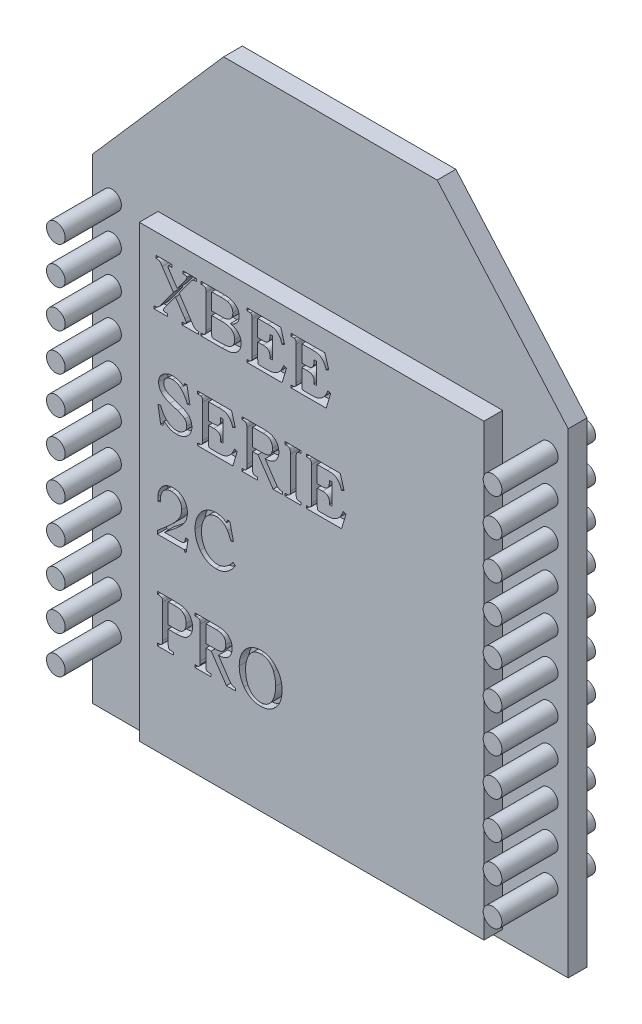
SolidWorks part; units mm, degrees
material "Custom Plastic"
ref_plane "Plan de face" through (0, 0, 0) normal (0, 0, 1) x (1, 0, 0)
ref_plane "Plan de dessus" through (0, 0, 0) normal (0, 1, 0) x (1, 0, 0)
ref_plane "Plan de droite" through (0, 0, 0) normal (1, 0, 0) x (0, 0, -1)
sketch "Esquisse1" plane through (0, 0, 0) normal (0, 0, 1) x (1, 0, 0)
  line L0 (0, 25.4) -> (7, 33.4)
  line L1 (0, 0) -> (25.4, 0)
  line L2 (0, 0) -> (0, 25.4)
  line L4 (25.4, 0) -> (25.4, 25.4)
  line L5 (7, 33.4) -> (18.4, 33.4)
  line L6 (18.4, 33.4) -> (25.4, 25.4)
  dimension "D1" = 7
  dimension "D2" = 7
  dimension "D3" = 25.4
  dimension "D4" = 25.4
  dimension "D5" = 8
  dimension "D6" = 8
extrude "Boss.-Extru.1" add sketch "Esquisse1" along normal blind 1
sketch "Esquisse2" plane through (0, 0, 1) normal (0, 0, 1) x (1, 0, 0)
  line L0 (0, 25.4) -> (0, 0) construction
  line L1 (3.5, 24.5) -> (21.9, 24.5)
  line L2 (3.5, 24.5) -> (3.5, 0.5)
  line L3 (3.5, 0.5) -> (21.9, 0.5)
  line L4 (21.9, 24.5) -> (21.9, 0.5)
  line L5 (25.4, 0) -> (25.4, 25.4) construction
  line L6 (0, 0) -> (25.4, 0) construction
  dimension "D1" = 3.5
  dimension "D2" = 3.5
  dimension "D3" = 24
  dimension "D4" = 0.5
extrude "Boss.-Extru.2" add sketch "Esquisse2" along normal blind 1
sketch3d "Esquisse3D1"
  line L0 (8.2324, 25.3977, 0) -> (8.2324, 25.3977, -3)
  line L1 (8.2324, 23.3977, -5) -> (8.2324, 10.3977, -5)
  arc A0 (8.2324, 25.3977, -3) -> (8.2324, 23.3977, -5) centre (8.2324, 23.3977, -3) ccw
  point P6 (8.2324, 25.3977, -5)
  point P7 (6.2324, 23.3977, -3)
  dimension "D3" = 2
  dimension "D1" = 5
  dimension "D2" = 0
  dimension "D4" = 15
sweep "Balayage1" add path "Esquisse3D1" circular profile diameter 1.5 parameters "D3"=1.5
sketch "Esquisse23" plane through (0, 10.3977, 0) normal (0, -1, 0) x (1, 0, 0)
  circle A0 centre (8.2324, -5) radius 1.5491
extrude "Boss.-Extru.4" add sketch "Esquisse23" along normal blind 7
fillet "Congé1" radius 1 1 edges at (8.2324, 3.3977, -6.5491)
sketch "Esquisse24" plane through (0, 0, 1) normal (0, 0, 1) x (1, 0, 0)
  line L1 (12.7, 36.8088) -> (12.7, -4.0108) construction
  circle A0 centre (1.0405, 23.7984) radius 0.5
  circle A1 centre (1.0405, 21.7984) radius 0.5
  circle A2 centre (1.0405, 19.7984) radius 0.5
  circle A3 centre (1.0405, 17.7984) radius 0.5
  circle A4 centre (1.0405, 15.7984) radius 0.5
  circle A5 centre (1.0405, 13.7984) radius 0.5
  circle A6 centre (1.0405, 11.7984) radius 0.5
  circle A7 centre (1.0405, 9.7984) radius 0.5
  circle A8 centre (1.0405, 7.7984) radius 0.5
  circle A9 centre (1.0405, 5.7984) radius 0.5
  circle A10 centre (1.0405, 3.7984) radius 0.5
  circle A11 centre (24.3595, 3.7984) radius 0.5
  circle A12 centre (24.3595, 5.7984) radius 0.5
  circle A13 centre (24.3595, 7.7984) radius 0.5
  circle A14 centre (24.3595, 9.7984) radius 0.5
  circle A15 centre (24.3595, 11.7984) radius 0.5
  circle A16 centre (24.3595, 13.7984) radius 0.5
  circle A17 centre (24.3595, 15.7984) radius 0.5
  circle A18 centre (24.3595, 17.7984) radius 0.5
  circle A19 centre (24.3595, 19.7984) radius 0.5
  circle A20 centre (24.3595, 21.7984) radius 0.5
  circle A21 centre (24.3595, 23.7984) radius 0.5
  dimension "D1" = 1
  dimension "D2" = 11
extrude "Boss.-Extru.5" add sketch "Esquisse24" along normal blind 3 and the other way blind 2
sketch "Esquisse25" plane through (0, 0, 2) normal (0, 0, 1) x (1, 0, 0)
  text T0 "XBEE\r\nSERIE\r\n2C \r\nPRO" font "Bookman Old Style" height in points 10
extrude "Enlèv. mat.-Extru.1" cut sketch "Esquisse25" against normal blind 0.5
